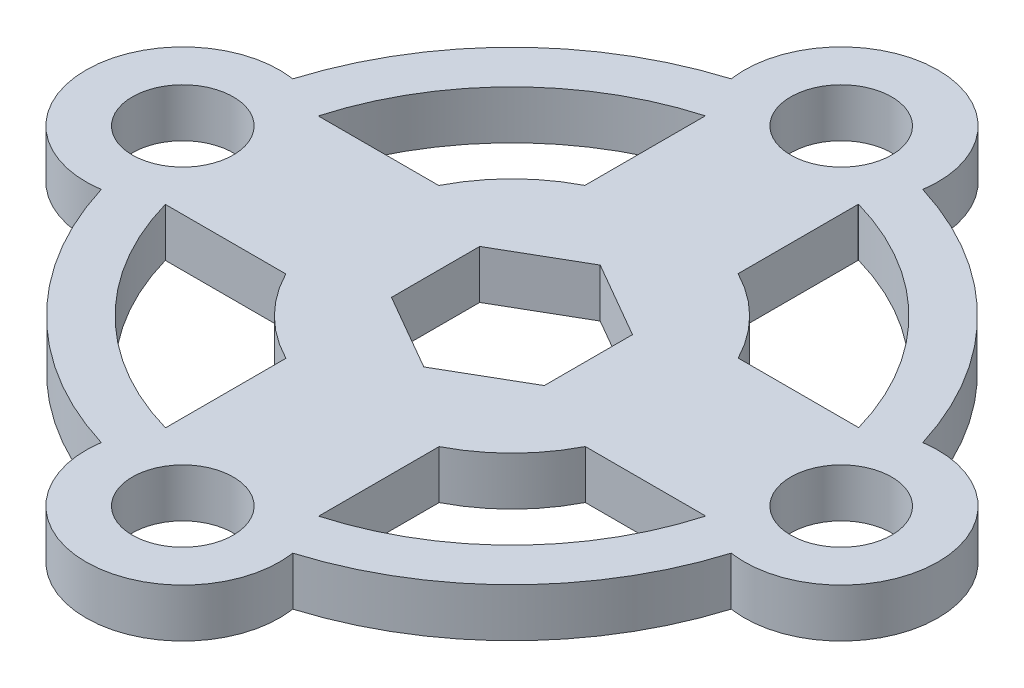
SolidWorks part; units mm, degrees
ref_plane "Front Plane" through (0, 0, 0) normal (0, 0, 1) x (1, 0, 0)
ref_plane "Top Plane" through (0, 0, 0) normal (0, 1, 0) x (1, 0, 0)
ref_plane "Right Plane" through (0, 0, 0) normal (1, 0, 0) x (0, 0, -1)
sketch "Sketch1" plane through (0, 0, 0) normal (0, 1, 0) x (1, 0, 0)
  line L0 (0, 0) -> (5, 0)
  line L1 (0, 5.7735) -> (-5, 2.8868)
  line L2 (-5, 2.8868) -> (-5, -2.8868)
  line L3 (-5, -2.8868) -> (0, -5.7735)
  line L4 (0, -5.7735) -> (5, -2.8868)
  line L5 (5, -2.8868) -> (5, 2.8868)
  line L6 (5, 2.8868) -> (0, 5.7735)
  line L7 (-5.0179, 17.6745) -> (-5.0179, 9.7888)
  line L8 (5, 17.6515) -> (5, 9.798)
  line L9 (17.6745, 5.0179) -> (9.7888, 5.0179)
  line L10 (17.6515, -5) -> (9.798, -5)
  line L11 (5.0179, -17.6745) -> (5.0179, -9.7888)
  line L12 (-5, -17.6515) -> (-5, -9.798)
  line L13 (-17.6745, -5.0179) -> (-9.7888, -5.0179)
  line L14 (-17.6515, 5) -> (-9.798, 5)
  circle A0 centre (0, 0) radius 11
  circle A1 centre (0, 0) radius 5 construction
  circle A2 centre (21.548, 0) radius 3.302
  circle A3 centre (21.548, 0) radius 6.339
  circle A4 centre (0, -21.548) radius 6.339
  circle A5 centre (0, -21.548) radius 3.302
  circle A6 centre (-21.548, 0) radius 6.339
  circle A7 centre (-21.548, 0) radius 3.302
  circle A8 centre (0, 21.548) radius 6.339
  circle A9 centre (0, 21.548) radius 3.302
  arc A10 (-6.2701, 20.6156) -> (-20.6156, 6.2701) centre (0, 0) ccw
  arc A11 (-17.6745, -5.0179) -> (-5.0179, -17.6745) centre (0, 0) ccw
  arc A12 (-20.6156, -6.2701) -> (-6.2701, -20.6156) centre (0, 0) ccw
  arc A13 (20.6156, 6.2701) -> (6.2701, 20.6156) centre (0, 0) ccw
  arc A14 (6.2701, -20.6156) -> (20.6156, -6.2701) centre (0, 0) ccw
  arc A15 (5.0179, -17.6745) -> (17.6745, -5.0179) centre (0, 0) ccw
  arc A16 (17.6745, 5.0179) -> (5.0179, 17.6745) centre (0, 0) ccw
  arc A17 (-5.0179, 17.6745) -> (-17.6745, 5.0179) centre (0, 0) ccw
  point P25 (0, 0)
  point P52 (0, 0)
  dimension "D1" = 21.548
  dimension "D2" = 6.604
  dimension "D3" = 4
  dimension "D5" = 12.678
  dimension "D6" = 21.548
  dimension "D4" = 4
extrude "Boss-Extrude1" add sketch "Sketch1" along normal blind 3.175 contours A17 A8 A10 A6 | A6 A7 | A6 A12 A4 A11 | A4 A5 | A6 L13 A0 L14 | A4 L11 A0 L12 | A0 L6 L5 L4 L3 L2 L1 | A8 L7 A0 L8 | A8 A9 | A16 A3 A13 A8 | A3 L9 A0 L10 | A3 A2 | A15 A4 A14 A3
